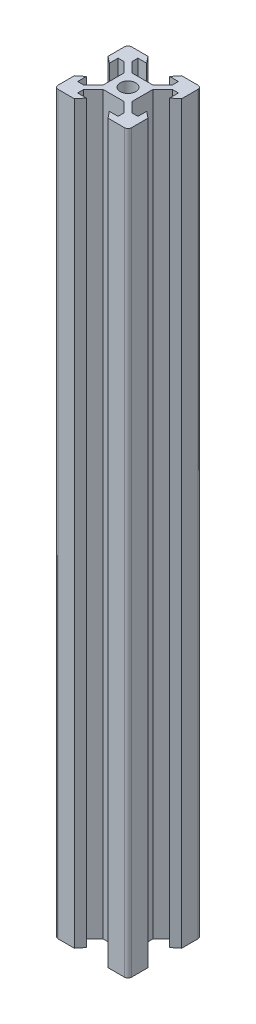
SolidWorks part; units mm, degrees
ref_plane "Front Plane" through (0, 0, 0) normal (0, 0, 1) x (1, 0, 0)
ref_plane "Top Plane" through (0, 0, 0) normal (0, 1, 0) x (1, 0, 0)
ref_plane "Right Plane" through (0, 0, 0) normal (1, 0, 0) x (0, 0, -1)
sketch "Sketch1" plane through (0, 0, 0) normal (0, 1, 0) x (1, 0, 0)
  line L0 (-3.125, 8.2) -> (-4.58, 10)
  line L1 (-9, 10) -> (9, 10)
  line L2 (-10, 9) -> (-10, -9)
  line L3 (-9, -10) -> (9, -10)
  line L4 (10, 9) -> (10, -9)
  line L5 (-10, 10) -> (10, -10) construction
  line L6 (-10, -10) -> (10, 10) construction
  line L7 (-10, 0) -> (0, 0) construction
  line L8 (0, 10) -> (0, 0) construction
  line L9 (-8.2, 3.125) -> (-10, 4.58)
  line L10 (-8.2, 3.125) -> (-8.2, 5.5)
  line L11 (-3.125, 8.2) -> (-5.5, 8.2)
  line L12 (-5.5, 8.2) -> (-5.5, 6.56)
  line L13 (-2.84, 3.9) -> (2.84, 3.9)
  line L14 (-5.5, 6.56) -> (-2.84, 3.9)
  line L15 (-8.2, 5.5) -> (-6.56, 5.5)
  line L16 (-6.56, 5.5) -> (-3.9, 2.84)
  line L17 (-3.9, 2.84) -> (-3.9, -2.84)
  line L18 (3.9, 2.84) -> (3.9, -2.84)
  line L19 (6.56, 5.5) -> (3.9, 2.84)
  line L20 (8.2, 5.5) -> (6.56, 5.5)
  line L21 (8.2, 3.125) -> (8.2, 5.5)
  line L22 (8.2, 3.125) -> (10, 4.58)
  line L23 (3.125, 8.2) -> (4.58, 10)
  line L24 (3.125, 8.2) -> (5.5, 8.2)
  line L25 (5.5, 8.2) -> (5.5, 6.56)
  line L26 (5.5, 6.56) -> (2.84, 3.9)
  line L27 (-8.2, -3.125) -> (-10, -4.58)
  line L28 (-8.2, -3.125) -> (-8.2, -5.5)
  line L29 (-8.2, -5.5) -> (-6.56, -5.5)
  line L30 (-6.56, -5.5) -> (-3.9, -2.84)
  line L31 (8.2, -3.125) -> (10, -4.58)
  line L32 (8.2, -3.125) -> (8.2, -5.5)
  line L33 (8.2, -5.5) -> (6.56, -5.5)
  line L34 (6.56, -5.5) -> (3.9, -2.84)
  line L35 (5.5, -6.56) -> (2.84, -3.9)
  line L36 (5.5, -8.2) -> (5.5, -6.56)
  line L37 (3.125, -8.2) -> (5.5, -8.2)
  line L38 (3.125, -8.2) -> (4.58, -10)
  line L39 (-5.5, -6.56) -> (-2.84, -3.9)
  line L40 (-2.84, -3.9) -> (2.84, -3.9)
  line L41 (-5.5, -8.2) -> (-5.5, -6.56)
  line L42 (-3.125, -8.2) -> (-5.5, -8.2)
  line L43 (-3.125, -8.2) -> (-4.58, -10)
  circle A0 centre (0, 0) radius 2.1
  arc A1 (-10, -9) -> (-9, -10) centre (-9, -9) ccw
  arc A2 (9, -10) -> (10, -9) centre (9, -9) ccw
  arc A3 (9, 10) -> (10, 9) centre (9, 9) cw
  arc A4 (-9, 10) -> (-10, 9) centre (-9, 9) ccw
  point P0 (0, 0)
  point P35 (0, 3.9)
  point P40 (-3.9, 0)
  point P41 (3.9, 0)
  dimension "D3" = 4.2
  dimension "D2" = 1
  dimension "D1" = 20
  dimension "D4" = 6.1
  dimension "D5" = 6.25
  dimension "D6" = 11
  dimension "D7" = 5.68
  dimension "D8" = 9.16
  dimension "D9" = 1.8
extrude "Boss-Extrude1" add sketch "Sketch1" along normal blind 200 contours L43 L42 L41 L39 L40 L35 L36 L37 L38 L3 L4 L31 L32 L33 L34 L18 L19 L20 L21 L22 L1 L23 L24 L25 L26 L13 L14 L12 L11 L0 L2 L9 L10 L15 L16 L17 L30 L29 L28 L27 A0
